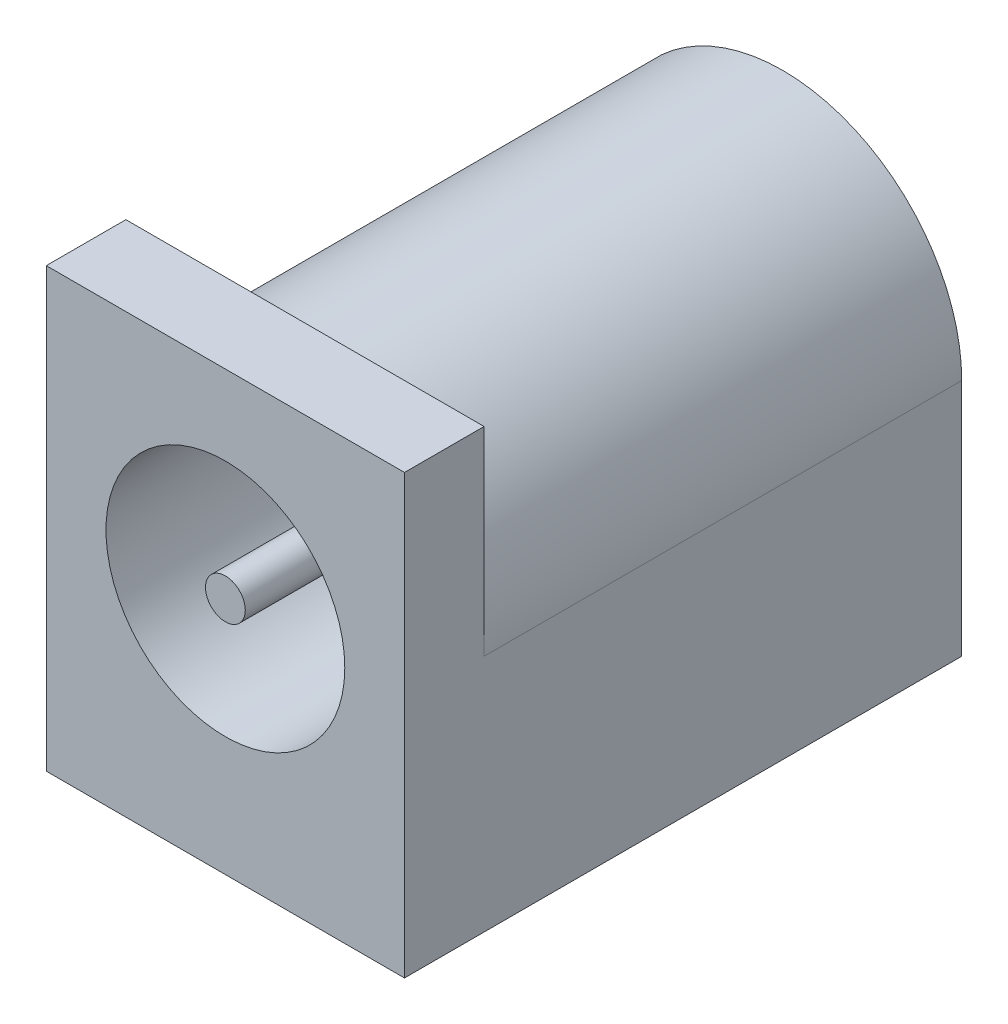
SolidWorks part; units mm, degrees
material "ABS"
ref_plane "Front Plane" through (0, 0, 0) normal (0, 0, 1) x (1, 0, 0)
ref_plane "Top Plane" through (0, 0, 0) normal (0, 1, 0) x (1, 0, 0)
ref_plane "Right Plane" through (0, 0, 0) normal (1, 0, 0) x (0, 0, -1)
sketch "Sketch1" plane through (0, 0, 0) normal (0, 0, 1) x (1, 0, 0)
  line L1 (-4.5, 5.5) -> (4.5, 5.5)
  line L2 (-4.5, 5.5) -> (-4.5, -5.5)
  line L3 (-4.5, -5.5) -> (4.5, -5.5)
  line L4 (4.5, 5.5) -> (4.5, -5.5)
  line L5 (-4.5, 5.5) -> (4.5, -5.5) construction
  line L6 (-4.5, -5.5) -> (4.5, 5.5) construction
  point P0 (0, 0)
  dimension "D1" = 9
  dimension "D2" = 11
extrude "Boss-Extrude1" add sketch "Sketch1" along normal blind 14
sketch "Sketch2" plane through (0, 0, 14) normal (0, 0, 1) x (1, 0, 0)
  line L0 (4.5, 5.5) -> (-4.5, 5.5) construction
  circle A0 centre (0, 0.5) radius 3
  dimension "D1" = 6
  dimension "D2" = 5
extrude "Cut-Extrude1" cut sketch "Sketch2" against normal blind 12
sketch "Sketch3" plane through (0, 0, 0) normal (0, 0, -1) x (-1, 0, 0)
  line L0 (-4.5, 5.5) -> (4.5, 5.5) construction
  line L1 (-4.5, 0.5) -> (-4.5, -5.5)
  line L2 (-4.5, -5.5) -> (4.5, -5.5)
  line L3 (4.5, -5.5) -> (4.5, 0.5)
  arc A0 (4.5, 0.5) -> (-4.5, 0.5) centre (0, 0.5) ccw
  dimension "D1" = 9
  dimension "D2" = 5
extrude "Cut-Extrude2" cut sketch "Sketch3" against normal blind 12 flip side to cut
sketch "Sketch4" plane through (0, 0, 2) normal (0, 0, 1) x (1, 0, 0)
  circle A0 centre (0, 0.5) radius 1
  dimension "D1" = 2
extrude "Boss-Extrude2" add sketch "Sketch4" along normal blind 2
sketch "Sketch5" plane through (0, 0, 4) normal (0, 0, 1) x (1, 0, 0)
  circle A0 centre (0, 0.5) radius 0.5
  dimension "D1" = 1
extrude "Boss-Extrude3" add sketch "Sketch5" along normal blind 10
